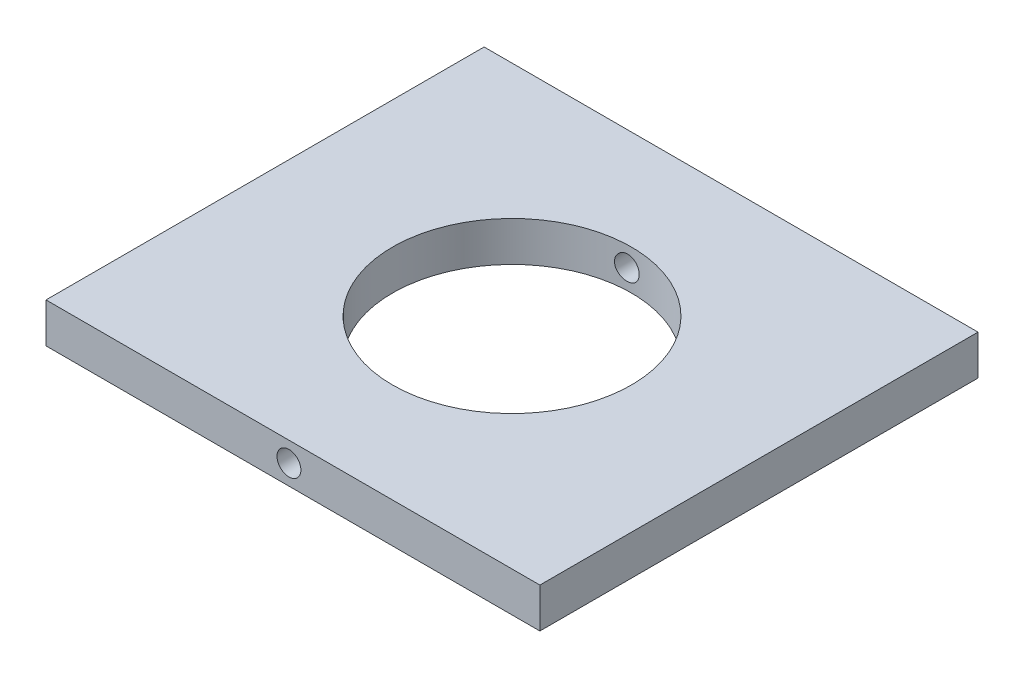
SolidWorks part; units mm, degrees
ref_plane "Plan de face" through (0, 0, 0) normal (0, 0, 1) x (1, 0, 0)
ref_plane "Plan de dessus" through (0, 0, 0) normal (0, 1, 0) x (1, 0, 0)
ref_plane "Plan de droite" through (0, 0, 0) normal (1, 0, 0) x (0, 0, -1)
sketch "Esquisse1" plane through (0, 0, 0) normal (0, 0, 1) x (1, 0, 0)
  line L0 (-9.5, -47.5) -> (52.5, -47.5) construction
  line L5 (-9.5, -45) -> (52.5, -45)
  line L6 (-9.5, -45) -> (-9.5, -50)
  line L7 (-9.5, -50) -> (52.5, -50)
  line L8 (52.5, -45) -> (52.5, -50)
  line L9 (21.5, -45) -> (21.5, -50) construction
  dimension "D1" = 5
  dimension "D2" = 62
extrude "Boss.-Extru.1" add sketch "Esquisse1" along normal blind 55
sketch "Esquisse2" plane through (0, -45, 0) normal (0, 1, 0) x (-1, 0, 0)
  line L0 (9.5, 55) -> (-52.5, 55) construction
  line L7 (-52.5, 55) -> (-52.5, 0) construction
  circle A0 centre (-21.5, 27.5) radius 15
  dimension "D10" = 31
  dimension "D11" = 27.5
extrude "Enlèv. mat.-Extru.1" cut sketch "Esquisse2" against normal through all
sketch "Esquisse5" plane through (0, 0, 55) normal (0, 0, 1) x (1, 0, 0)
  line L0 (-9.5, -45) -> (52.5, -45) construction
  line L1 (-9.5, -45) -> (-9.5, -50) construction
  circle A0 centre (21, -47.5) radius 1.5
  dimension "D1" = 2.5
  dimension "D2" = 30.5
extrude "Enlèv. mat.-Extru.4" cut sketch "Esquisse5" against normal through all
